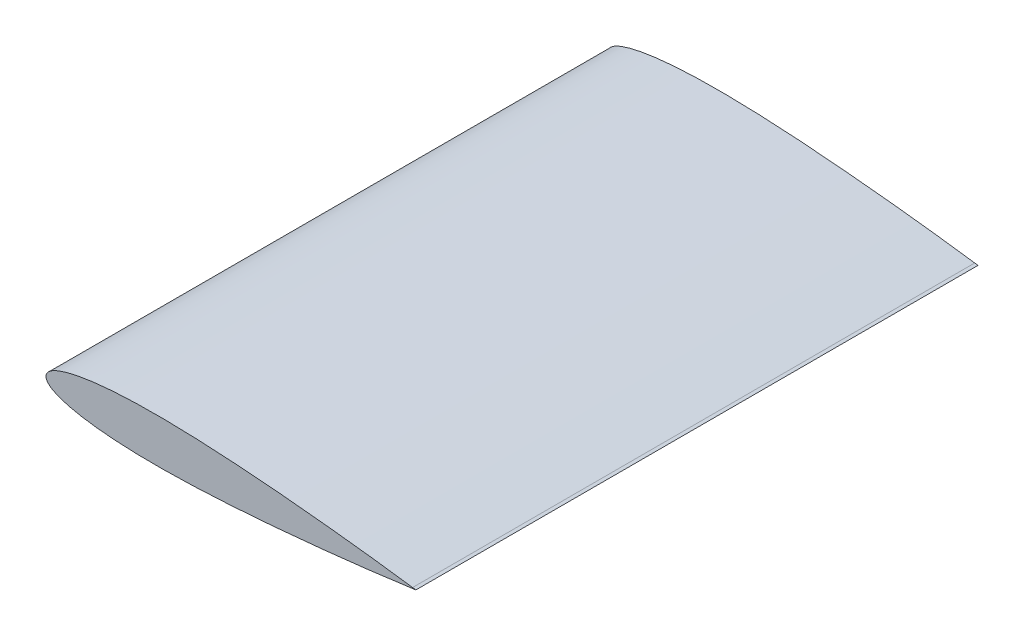
SolidWorks part; units mm, degrees
material "Default"
ref_plane "Front Plane" through (0, 0, 0) normal (0, 0, 1) x (1, 0, 0)
ref_plane "Top Plane" through (0, 0, 0) normal (0, 1, 0) x (1, 0, 0)
ref_plane "Right Plane" through (0, 0, 0) normal (1, 0, 0) x (0, 0, -1)
curve "Curve1"
  spline degree 3 poles (150, 0.189, 0) (149.9708, 0.1931, 0) (149.8541, 0.2095, 0) (149.5918, 0.2462, 0) (149.1552, 0.3072, 0) (148.5455, 0.392, 0) (147.764, 0.5, 0) (146.8126, 0.6306, 0) (145.6934, 0.783, 0) (144.4092, 0.9561, 0) (142.9628, 1.149, 0) (141.3577, 1.3605, 0) (139.5976, 1.5893, 0) (137.6867, 1.8342, 0) (135.6293, 2.0938, 0) (133.4304, 2.3666, 0) (131.0949, 2.6514, 0) (128.6285, 2.9467, 0) (126.0368, 3.2508, 0) (123.3259, 3.5625, 0) (120.5021, 3.8802, 0) (117.5721, 4.2023, 0) (114.5427, 4.5273, 0) (111.4208, 4.8538, 0) (108.214, 5.18, 0) (104.9295, 5.5044, 0) (101.5752, 5.8254, 0) (98.1588, 6.1412, 0) (94.6883, 6.4501, 0) (91.1718, 6.7503, 0) (87.6175, 7.0401, 0) (84.0338, 7.3174, 0) (80.429, 7.5805, 0) (76.8115, 7.8274, 0) (73.1897, 8.0562, 0) (69.5722, 8.2648, 0) (65.9673, 8.4514, 0) (62.3836, 8.6142, 0) (58.8292, 8.7511, 0) (55.3127, 8.8605, 0) (51.842, 8.9408, 0) (48.4255, 8.9904, 0) (45.071, 9.0081, 0) (41.7863, 8.9926, 0) (38.5792, 8.943, 0) (35.4572, 8.8586, 0) (32.4274, 8.7389, 0) (29.497, 8.5837, 0) (26.6728, 8.3929, 0) (23.9615, 8.1668, 0) (21.3693, 7.906, 0) (18.9022, 7.6113, 0) (16.566, 7.2836, 0) (14.3662, 6.9241, 0) (12.3078, 6.5342, 0) (10.3956, 6.1153, 0) (8.6338, 5.6693, 0) (7.0266, 5.1976, 0) (5.5775, 4.7022, 0) (4.2895, 4.1845, 0) (3.1652, 3.6463, 0) (2.2066, 3.0886, 0) (1.4152, 2.5122, 0) (0.7919, 1.9165, 0) (0.339, 1.2993, 0) (0.0618, 0.658, 0) (-0.0301, 0, 0) (0.0618, -0.658, 0) (0.339, -1.2993, 0) (0.7919, -1.9165, 0) (1.4152, -2.5122, 0) (2.2066, -3.0886, 0) (3.1652, -3.6463, 0) (4.2895, -4.1845, 0) (5.5775, -4.7022, 0) (7.0266, -5.1976, 0) (8.6338, -5.6693, 0) (10.3956, -6.1153, 0) (12.3078, -6.5342, 0) (14.3662, -6.9241, 0) (16.566, -7.2836, 0) (18.9022, -7.6113, 0) (21.3693, -7.906, 0) (23.9615, -8.1668, 0) (26.6728, -8.3929, 0) (29.497, -8.5837, 0) (32.4274, -8.7389, 0) (35.4572, -8.8586, 0) (38.5792, -8.943, 0) (41.7863, -8.9926, 0) (45.071, -9.0081, 0) (48.4255, -8.9904, 0) (51.842, -8.9408, 0) (55.3127, -8.8605, 0) (58.8292, -8.7511, 0) (62.3836, -8.6142, 0) (65.9673, -8.4514, 0) (69.5722, -8.2648, 0) (73.1897, -8.0562, 0) (76.8115, -7.8274, 0) (80.429, -7.5805, 0) (84.0338, -7.3174, 0) (87.6175, -7.0401, 0) (91.1718, -6.7503, 0) (94.6883, -6.4501, 0) (98.1588, -6.1412, 0) (101.5752, -5.8254, 0) (104.9295, -5.5044, 0) (108.214, -5.18, 0) (111.4208, -4.8538, 0) (114.5427, -4.5273, 0) (117.5721, -4.2023, 0) (120.5021, -3.8802, 0) (123.3259, -3.5625, 0) (126.0368, -3.2508, 0) (128.6285, -2.9467, 0) (131.0949, -2.6514, 0) (133.4304, -2.3666, 0) (135.6293, -2.0938, 0) (137.6867, -1.8342, 0) (139.5976, -1.5893, 0) (141.3577, -1.3605, 0) (142.9628, -1.149, 0) (144.4092, -0.9561, 0) (145.6934, -0.783, 0) (146.8126, -0.6306, 0) (147.764, -0.5, 0) (148.5455, -0.392, 0) (149.1552, -0.3072, 0) (149.5918, -0.2462, 0) (149.8541, -0.2095, 0) (149.9708, -0.1931, 0) (150, -0.189, 0) knots 0 0 0 0 0.000289 0.001156 0.002598 0.004612 0.007194 0.010336 0.014031 0.018271 0.023046 0.028343 0.03415 0.040454 0.047239 0.054489 0.062186 0.070314 0.078852 0.08778 0.097077 0.106722 0.116691 0.126961 0.137507 0.148306 0.159331 0.170557 0.181957 0.193504 0.205172 0.216932 0.228758 0.240621 0.252495 0.26435 0.276161 0.287898 0.299536 0.311047 0.322405 0.333584 0.344559 0.355306 0.3658 0.376018 0.385938 0.395538 0.404798 0.413699 0.422222 0.430349 0.438066 0.445357 0.452209 0.458611 0.464554 0.47003 0.475035 0.479569 0.483637 0.48725 0.490431 0.493219 0.495674 0.497891 0.5 0.502109 0.504326 0.506781 0.509569 0.51275 0.516363 0.520431 0.524965 0.52997 0.535446 0.541389 0.547791 0.554643 0.561934 0.569651 0.577778 0.586301 0.595202 0.604462 0.614062 0.623982 0.6342 0.644694 0.655441 0.666416 0.677595 0.688953 0.700464 0.712102 0.723839 0.73565 0.747505 0.759379 0.771242 0.783068 0.794828 0.806496 0.818043 0.829443 0.840669 0.851694 0.862493 0.873039 0.883309 0.893278 0.902923 0.91222 0.921148 0.929686 0.937814 0.945511 0.952761 0.959546 0.96585 0.971657 0.976954 0.981729 0.985969 0.989664 0.992806 0.995388 0.997402 0.998844 0.999711 1 1 1 1
sketch "Sketch3" plane through (0, 0, 0) normal (0, 0, 1) x (1, 0, 0)
  line L0 (150, 0.189) -> (151.3472, 0)
  line L1 (150, -0.189) -> (151.3472, 0)
  spline S0 degree 3 poles (664.8157, 2954.4251) (215.4039, -11.6719) (182.7566, -4.3968) (149.5918, 0.2462) (149.1552, 0.3072) (148.5455, 0.392) (147.764, 0.5) (146.8126, 0.6306) (145.6934, 0.783) (144.4092, 0.9561) (142.9628, 1.149) (141.3577, 1.3605) (139.5976, 1.5893) (137.6867, 1.8342) (135.6293, 2.0938) (133.4304, 2.3666) (131.0949, 2.6514) (128.6285, 2.9467) (126.0368, 3.2508) (123.3259, 3.5625) (120.5021, 3.8802) (117.5721, 4.2023) (113.4735, 4.6421) (109.256, 5.0771) (104.9295, 5.5044) (101.5752, 5.8254) (98.1588, 6.1412) (94.6883, 6.4501) (91.1718, 6.7503) (87.6175, 7.0401) (84.0338, 7.3174) (80.429, 7.5805) (76.8115, 7.8274) (73.1897, 8.0562) (69.5722, 8.2648) (65.9673, 8.4514) (62.3836, 8.6142) (58.8292, 8.7511) (55.3127, 8.8605) (51.842, 8.9408) (48.4255, 8.9904) (45.071, 9.0081) (41.7863, 8.9926) (38.5792, 8.943) (35.4572, 8.8586) (32.4274, 8.7389) (29.497, 8.5837) (26.6728, 8.3929) (23.9615, 8.1668) (21.3693, 7.906) (18.9022, 7.6113) (16.566, 7.2836) (14.3662, 6.9241) (12.3078, 6.5342) (10.3956, 6.1153) (8.6338, 5.6693) (7.0266, 5.1976) (5.5775, 4.7022) (4.2895, 4.1845) (3.1652, 3.6463) (2.2066, 3.0886) (1.4152, 2.5122) (0.7919, 1.9165) (0.339, 1.2993) (0.0618, 0.658) (-0.0301, 0) (0.0618, -0.658) (0.339, -1.2993) (0.7919, -1.9165) (1.4152, -2.5122) (2.2066, -3.0886) (3.1652, -3.6463) (4.2895, -4.1845) (5.5775, -4.7022) (7.0266, -5.1976) (8.6338, -5.6693) (10.3956, -6.1153) (12.3078, -6.5342) (14.3662, -6.9241) (16.566, -7.2836) (18.9022, -7.6113) (21.3693, -7.906) (23.9615, -8.1668) (26.6728, -8.3929) (29.497, -8.5837) (32.4274, -8.7389) (35.4572, -8.8586) (38.5792, -8.943) (41.7863, -8.9926) (45.071, -9.0081) (48.4255, -8.9904) (51.842, -8.9408) (55.3127, -8.8605) (58.8292, -8.7511) (62.3836, -8.6142) (65.9673, -8.4514) (69.5722, -8.2648) (73.1897, -8.0562) (76.8115, -7.8274) (80.429, -7.5805) (84.0338, -7.3174) (87.6175, -7.0401) (91.1718, -6.7503) (94.6883, -6.4501) (98.1588, -6.1412) (102.6715, -5.724) (108.1378, -5.1924) (113.4735, -4.6421) (117.5721, -4.2023) (120.5021, -3.8802) (123.3259, -3.5625) (126.0368, -3.2508) (128.6285, -2.9467) (131.0949, -2.6514) (133.4304, -2.3666) (135.6293, -2.0938) (137.6867, -1.8342) (139.5976, -1.5893) (141.3577, -1.3605) (142.9628, -1.149) (144.4092, -0.9561) (145.6934, -0.783) (146.8126, -0.6306) (147.764, -0.5) (148.5455, -0.392) (149.1552, -0.3072) (149.5918, -0.2462) (182.7561, 4.3968) (215.403, 11.6717) (664.7971, -2954.3028) knots -0.325853 -0.325853 -0.325853 -0.325853 0.000289 0.001156 0.002598 0.004612 0.007194 0.010336 0.014031 0.018271 0.023046 0.028343 0.03415 0.040454 0.047239 0.054489 0.062186 0.070314 0.078852 0.08778 0.097077 0.106722 0.116691 0.137507 0.148306 0.159331 0.170557 0.181957 0.193504 0.205172 0.216932 0.228758 0.240621 0.252495 0.26435 0.276161 0.287898 0.299536 0.311047 0.322405 0.333584 0.344559 0.355306 0.3658 0.376018 0.385938 0.395538 0.404798 0.413699 0.422222 0.430349 0.438066 0.445357 0.452209 0.458611 0.464554 0.47003 0.475035 0.479569 0.483637 0.48725 0.490431 0.493219 0.495674 0.497891 0.5 0.502109 0.504326 0.506781 0.509569 0.51275 0.516363 0.520431 0.524965 0.52997 0.535446 0.541389 0.547791 0.554643 0.561934 0.569651 0.577778 0.586301 0.595202 0.604462 0.614062 0.623982 0.6342 0.644694 0.655441 0.666416 0.677595 0.688953 0.700464 0.712102 0.723839 0.73565 0.747505 0.759379 0.771242 0.783068 0.794828 0.806496 0.818043 0.829443 0.840669 0.862493 0.883309 0.893278 0.902923 0.91222 0.921148 0.929686 0.937814 0.945511 0.952761 0.959546 0.96585 0.971657 0.976954 0.981729 0.985969 0.989664 0.992806 0.995388 0.997402 0.998844 0.999711 1.325848 1.325848 1.325848 1.325848 only from (150, 0.189) to (150, -0.189) construction
  spline S1 degree 3 poles (150, 0.189) (149.9708, 0.1931) (149.8541, 0.2095) (149.5918, 0.2462) (149.1552, 0.3072) (148.5455, 0.392) (147.764, 0.5) (146.8126, 0.6306) (145.6934, 0.783) (144.4092, 0.9561) (142.9628, 1.149) (141.3577, 1.3605) (139.5976, 1.5893) (137.6867, 1.8342) (135.6293, 2.0938) (133.4304, 2.3666) (131.0949, 2.6514) (128.6285, 2.9467) (126.0368, 3.2508) (123.3259, 3.5625) (120.5021, 3.8802) (117.5721, 4.2023) (113.4735, 4.6421) (109.256, 5.0771) (104.9295, 5.5044) (101.5752, 5.8254) (98.1588, 6.1412) (94.6883, 6.4501) (91.1718, 6.7503) (87.6175, 7.0401) (84.0338, 7.3174) (80.429, 7.5805) (76.8115, 7.8274) (73.1897, 8.0562) (69.5722, 8.2648) (65.9673, 8.4514) (62.3836, 8.6142) (58.8292, 8.7511) (55.3127, 8.8605) (51.842, 8.9408) (48.4255, 8.9904) (45.071, 9.0081) (41.7863, 8.9926) (38.5792, 8.943) (35.4572, 8.8586) (32.4274, 8.7389) (29.497, 8.5837) (26.6728, 8.3929) (23.9615, 8.1668) (21.3693, 7.906) (18.9022, 7.6113) (16.566, 7.2836) (14.3662, 6.9241) (12.3078, 6.5342) (10.3956, 6.1153) (8.6338, 5.6693) (7.0266, 5.1976) (5.5775, 4.7022) (4.2895, 4.1845) (3.1652, 3.6463) (2.2066, 3.0886) (1.4152, 2.5122) (0.7919, 1.9165) (0.339, 1.2993) (0.0618, 0.658) (-0.0301, 0) (0.0618, -0.658) (0.339, -1.2993) (0.7919, -1.9165) (1.4152, -2.5122) (2.2066, -3.0886) (3.1652, -3.6463) (4.2895, -4.1845) (5.5775, -4.7022) (7.0266, -5.1976) (8.6338, -5.6693) (10.3956, -6.1153) (12.3078, -6.5342) (14.3662, -6.9241) (16.566, -7.2836) (18.9022, -7.6113) (21.3693, -7.906) (23.9615, -8.1668) (26.6728, -8.3929) (29.497, -8.5837) (32.4274, -8.7389) (35.4572, -8.8586) (38.5792, -8.943) (41.7863, -8.9926) (45.071, -9.0081) (48.4255, -8.9904) (51.842, -8.9408) (55.3127, -8.8605) (58.8292, -8.7511) (62.3836, -8.6142) (65.9673, -8.4514) (69.5722, -8.2648) (73.1897, -8.0562) (76.8115, -7.8274) (80.429, -7.5805) (84.0338, -7.3174) (87.6175, -7.0401) (91.1718, -6.7503) (94.6883, -6.4501) (98.1588, -6.1412) (102.6715, -5.724) (108.1378, -5.1924) (113.4735, -4.6421) (117.5721, -4.2023) (120.5021, -3.8802) (123.3259, -3.5625) (126.0368, -3.2508) (128.6285, -2.9467) (131.0949, -2.6514) (133.4304, -2.3666) (135.6293, -2.0938) (137.6867, -1.8342) (139.5976, -1.5893) (141.3577, -1.3605) (142.9628, -1.149) (144.4092, -0.9561) (145.6934, -0.783) (146.8126, -0.6306) (147.764, -0.5) (148.5455, -0.392) (149.1552, -0.3072) (149.5918, -0.2462) (149.8541, -0.2095) (149.9708, -0.1931) (150, -0.189) knots 0 0 0 0 0.000289 0.001156 0.002598 0.004612 0.007194 0.010336 0.014031 0.018271 0.023046 0.028343 0.03415 0.040454 0.047239 0.054489 0.062186 0.070314 0.078852 0.08778 0.097077 0.106722 0.116691 0.137507 0.148306 0.159331 0.170557 0.181957 0.193504 0.205172 0.216932 0.228758 0.240621 0.252495 0.26435 0.276161 0.287898 0.299536 0.311047 0.322405 0.333584 0.344559 0.355306 0.3658 0.376018 0.385938 0.395538 0.404798 0.413699 0.422222 0.430349 0.438066 0.445357 0.452209 0.458611 0.464554 0.47003 0.475035 0.479569 0.483637 0.48725 0.490431 0.493219 0.495674 0.497891 0.5 0.502109 0.504326 0.506781 0.509569 0.51275 0.516363 0.520431 0.524965 0.52997 0.535446 0.541389 0.547791 0.554643 0.561934 0.569651 0.577778 0.586301 0.595202 0.604462 0.614062 0.623982 0.6342 0.644694 0.655441 0.666416 0.677595 0.688953 0.700464 0.712102 0.723839 0.73565 0.747505 0.759379 0.771242 0.783068 0.794828 0.806496 0.818043 0.829443 0.840669 0.862493 0.883309 0.893278 0.902923 0.91222 0.921148 0.929686 0.937814 0.945511 0.952761 0.959546 0.96585 0.971657 0.976954 0.981729 0.985969 0.989664 0.992806 0.995388 0.997402 0.998844 0.999711 1 1 1 1
extrude "Boss-Extrude2" add sketch "Sketch3" along normal mid plane 230
